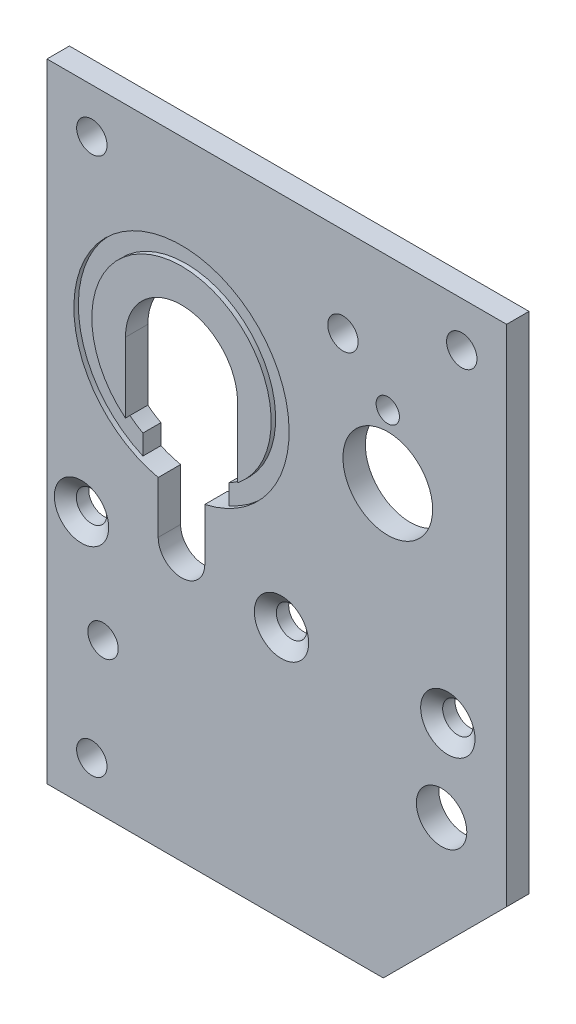
SolidWorks part; units mm, degrees
material "Acrylic (Medium-high impact)"
ref_plane "Front Plane" through (0, 0, 0) normal (0, 0, 1) x (1, 0, 0)
ref_plane "Top Plane" through (0, 0, 0) normal (0, 1, 0) x (1, 0, 0)
ref_plane "Right Plane" through (0, 0, 0) normal (1, 0, 0) x (0, 0, -1)
sketch "Sketch1" plane through (0, 0, 0) normal (0, 0, 1) x (1, 0, 0)
  line L5 (-65.0875, 0) -> (-65.0875, -88.9)
  line L6 (-65.0875, -88.9) -> (-17.4625, -88.9)
  line L7 (-17.4625, -88.9) -> (0, -71.4375)
  line L8 (0, -71.4375) -> (0, 0)
  line L9 (0, 0) -> (-65.0875, 0)
  line L10 (-65.0875, 0) -> (-65.0875, -88.9)
  line L11 (-65.0875, -88.9) -> (-17.4625, -88.9)
  line L12 (-17.4625, -88.9) -> (0, -71.4375)
  line L13 (0, -71.4375) -> (0, 0)
  line L14 (0, 0) -> (-65.0875, 0)
  dimension "D1" = 0
extrude "Boss-Extrude1" add sketch "Sketch1" against normal blind 3.175
hole_wizard "#6 Clearance Hole1" positions "Sketch3" profile "Sketch2" hole size "#6" standard "ANSI Inch" end condition through all
sketch "Sketch3" plane through (0, 0, 0) normal (0, 0, 1) x (1, 0, 0)
  point P0 (-58.7375, -6.35)
  point P3 (-6.35, -6.35)
  point P6 (-23.1775, -12.7)
  point P9 (-57.15, -67.31)
  point P12 (-58.7375, -82.55)
sketch "Sketch2" plane through (-58.7375, -6.35, 0) normal (1, 0, 0) x (0, -1, 0)
  line L0 (0, 0) -> (0, 3.175)
  line L1 (0, 3.175) -> (2.1526, 3.175)
  line L2 (2.1526, 3.175) -> (2.1526, 0)
  line L5 (2.1526, 0) -> (0, 0)
  line L11 (0, -6.35) -> (0, 107.95) construction
  dimension "Thru Hole Dia." = 4.3053
  dimension "Thru Hole Depth" = 3.175
sketch "Sketch4" plane through (0, 0, 0) normal (0, 0, 1) x (1, 0, 0)
  line L0 (-49.3395, -50.8) -> (-49.3395, -43.453) construction
  line L1 (-42.7355, -43.453) -> (-42.7355, -50.8) construction
  line L2 (-49.3395, -50.8) -> (-49.3395, -43.453)
  line L3 (-42.7355, -43.453) -> (-42.7355, -50.8)
  arc A0 (-42.7355, -43.453) -> (-49.3395, -43.453) centre (-46.0375, -28.575) ccw construction
  arc A1 (-49.3395, -50.8) -> (-42.7355, -50.8) centre (-46.0375, -50.8) ccw construction
  arc A2 (-42.7355, -43.453) -> (-49.3395, -43.453) centre (-46.0375, -28.575) ccw
  arc A3 (-49.3395, -50.8) -> (-42.7355, -50.8) centre (-46.0375, -50.8) ccw
extrude "Cut-Extrude1" cut sketch "Sketch4" against normal through all
sketch "Sketch5" plane through (0, 0, 0) normal (0, 0, 1) x (1, 0, 0)
  circle A0 centre (-16.8275, -27.94) radius 6.35
  circle A1 centre (-16.8275, -18.9484) radius 1.651
  dimension "D1" = 12.7
  dimension "D2" = 3.302
  dimension "D3" = 8.9916
extrude "Cut-Extrude2" cut sketch "Sketch5" against normal through all
hole_wizard "1/4 Clearance Hole1" positions "Sketch7" profile "Sketch6" hole size "1/4" standard "ANSI Inch" end condition through all
sketch "Sketch7" plane through (0, 0, 0) normal (0, 0, 1) x (1, 0, 0)
  point P0 (-9.2075, -65.0875)
sketch "Sketch6" plane through (-9.2075, -65.0875, 0) normal (1, 0, 0) x (0, -1, 0)
  line L0 (0, 0) -> (0, 3.175)
  line L1 (0, 3.175) -> (3.5712, 3.175)
  line L2 (3.5712, 3.175) -> (3.5712, 0)
  line L5 (3.5712, 0) -> (0, 0)
  line L11 (0, -6.35) -> (0, 107.95) construction
  dimension "Thru Hole Dia." = 7.1425
  dimension "Thru Hole Depth" = 3.175
sketch "Sketch8" plane through (0, 0, -3.175) normal (0, 0, -1) x (-1, 0, 0)
  line L0 (52.1335, -39.7163) -> (52.1335, -42.5427) construction
  line L1 (53.975, -28.575) -> (53.975, -38.4889) construction
  line L2 (38.1, -38.4889) -> (38.1, -28.575) construction
  line L3 (39.9415, -42.5427) -> (39.9415, -39.7163) construction
  line L4 (52.1335, -39.7163) -> (52.1335, -42.5427)
  line L5 (53.975, -28.575) -> (53.975, -38.4889)
  line L6 (38.1, -38.4889) -> (38.1, -28.575)
  line L7 (39.9415, -42.5427) -> (39.9415, -39.7163)
  arc A0 (52.1335, -39.7163) -> (53.975, -38.4889) centre (46.0375, -28.575) ccw construction
  arc A1 (53.975, -28.575) -> (38.1, -28.575) centre (46.0375, -28.575) ccw construction
  arc A2 (38.1, -38.4889) -> (39.9415, -39.7163) centre (46.0375, -28.575) ccw construction
  arc A3 (49.3395, -43.453) -> (42.7355, -43.453) centre (46.0375, -28.575) ccw construction
  arc A4 (52.1335, -39.7163) -> (53.975, -38.4889) centre (46.0375, -28.575) ccw
  arc A5 (53.975, -28.575) -> (38.1, -28.575) centre (46.0375, -28.575) ccw
  arc A6 (38.1, -38.4889) -> (39.9415, -39.7163) centre (46.0375, -28.575) ccw
  arc A7 (52.1335, -42.5427) -> (39.9415, -42.5427) centre (46.0375, -28.575) ccw
extrude "Boss-Extrude2" add sketch "Sketch8" against normal through all
sketch "Sketch9" plane through (0, 0, 0) normal (0, 0, 1) x (1, 0, 0)
  line L0 (-52.1335, -39.7163) -> (-52.1335, -42.5427) construction
  line L1 (-39.9415, -42.5427) -> (-39.9415, -39.7163) construction
  line L2 (-52.1335, -39.7163) -> (-52.1335, -42.5427)
  line L3 (-39.9415, -42.5427) -> (-39.9415, -39.7163)
  arc A0 (-42.7355, -43.453) -> (-49.3395, -43.453) centre (-46.0375, -28.575) ccw construction
  arc A1 (-53.975, -38.4889) -> (-52.1335, -39.7163) centre (-46.0375, -28.575) ccw construction
  arc A2 (-38.1, -38.4889) -> (-53.975, -38.4889) centre (-46.0375, -28.575) ccw construction
  arc A3 (-39.9415, -39.7163) -> (-38.1, -38.4889) centre (-46.0375, -28.575) ccw construction
  arc A4 (-39.9415, -42.5427) -> (-52.1335, -42.5427) centre (-46.0375, -28.575) ccw
  arc A5 (-53.975, -38.4889) -> (-52.1335, -39.7163) centre (-46.0375, -28.575) ccw
  arc A6 (-38.1, -38.4889) -> (-53.975, -38.4889) centre (-46.0375, -28.575) ccw
  arc A7 (-39.9415, -39.7163) -> (-38.1, -38.4889) centre (-46.0375, -28.575) ccw
extrude "Cut-Extrude3" cut sketch "Sketch9" against normal blind 0.635
hole_wizard "CSK for #6 Flat Head Machine Screw (100)1" positions "Sketch11" profile "Sketch10" countersink size "#6" standard "ANSI Inch" end condition through all
sketch "Sketch11" plane through (0, 0, 0) normal (0, 0, 1) x (1, 0, 0)
  point P1 (-31.877, -53.0919)
  point P5 (-60.198, -53.0919)
  point P8 (-8.321, -53.0919)
sketch "Sketch10" plane through (-31.877, -53.0919, 0) normal (1, 0, 0) x (0, -1, 0)
  line L0 (0, 0) -> (0, 3.175)
  line L1 (0, 3.175) -> (2.1526, 3.175)
  line L2 (2.1526, 3.175) -> (2.1526, 1.4209)
  line L3 (2.1526, 1.4209) -> (3.846, 0)
  line L5 (3.846, 0) -> (0, 0)
  line L6 (-2.1526, 1.4209) -> (-3.846, 0) construction
  line L11 (0, -6.35) -> (0, 107.95) construction
  dimension "Thru Hole Dia." = 4.3053
  dimension "Thru Hole Depth" = 3.175
  dimension "Near C'Sink Dia." = 7.692
  dimension "Near C'Sink Angle" = 100
